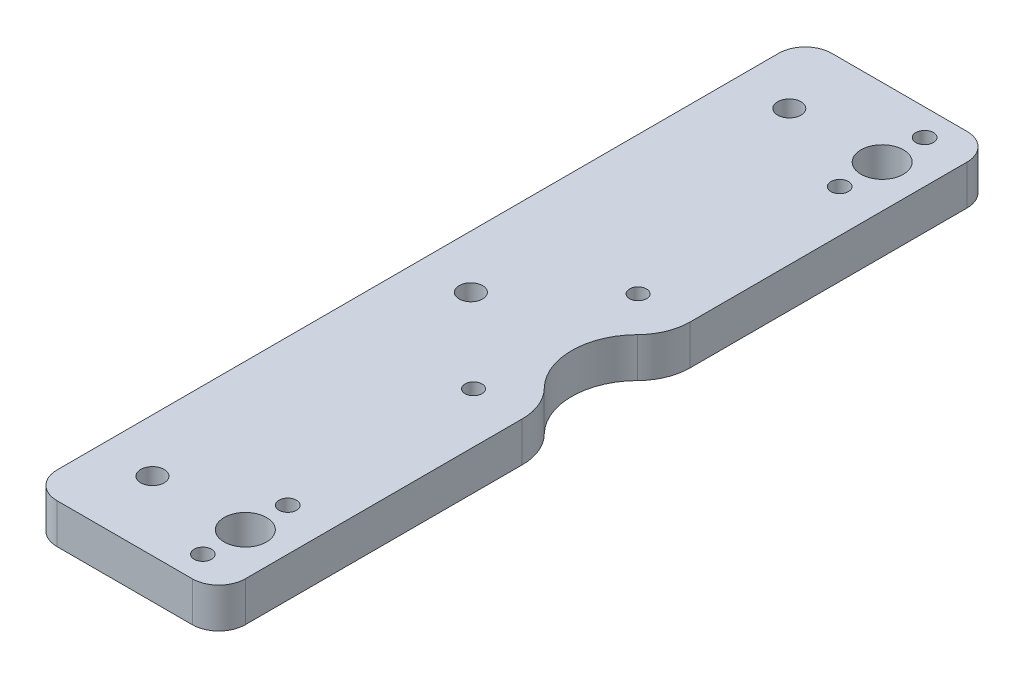
SolidWorks part; units mm, degrees
ref_plane "Front Plane" through (0, 0, 0) normal (0, 0, 1) x (1, 0, 0)
ref_plane "Top Plane" through (0, 0, 0) normal (0, 1, 0) x (1, 0, 0)
ref_plane "Right Plane" through (0, 0, 0) normal (1, 0, 0) x (0, 0, -1)
ref_plane "Plane1" through (0, 3.75, 0) normal (0, 1, 0) x (1, 0, 0)
sketch "Sketch1" plane through (0, 3.75, 0) normal (0, 1, 0) x (1, 0, 0)
  line L0 (8, -68) -> (8, -15.8193)
  line L1 (8, 15.8193) -> (8, 68)
  line L2 (3, 73) -> (-22.5, 73)
  line L3 (-27.5, 68) -> (-27.5, -68)
  line L4 (-22.5, -73) -> (3, -73)
  arc A0 (8, -15.8193) -> (5.1111, -8.7885) centre (-2, -15.8193) ccw
  arc A1 (5.1111, -8.7885) -> (5.1111, 8.7885) centre (14, 0) cw
  arc A2 (5.1111, 8.7885) -> (8, 15.8193) centre (-2, 15.8193) ccw
  arc A3 (8, 68) -> (3, 73) centre (3, 68) ccw
  arc A4 (-22.5, 73) -> (-27.5, 68) centre (-22.5, 68) ccw
  arc A5 (-27.5, -68) -> (-22.5, -73) centre (-22.5, -68) ccw
  arc A6 (3, -73) -> (8, -68) centre (3, -68) ccw
  circle A7 centre (0, -68) radius 1.65
  circle A8 centre (0, -52) radius 1.65
  circle A9 centre (0, 68) radius 1.65
  circle A10 centre (0, 52) radius 1.65
  circle A11 centre (-1.5, 15.5) radius 1.6
  circle A12 centre (-1.5, -15.5) radius 1.6
  circle A13 centre (-17.5, 0) radius 2.2
  circle A14 centre (0, -60) radius 4
  circle A15 centre (0, 60) radius 4
  circle A16 centre (-17.5, 60) radius 2.2
  circle A17 centre (-17.5, -60) radius 2.2
extrude "Boss-Extrude1" add sketch "Sketch1" against normal blind 7.5
